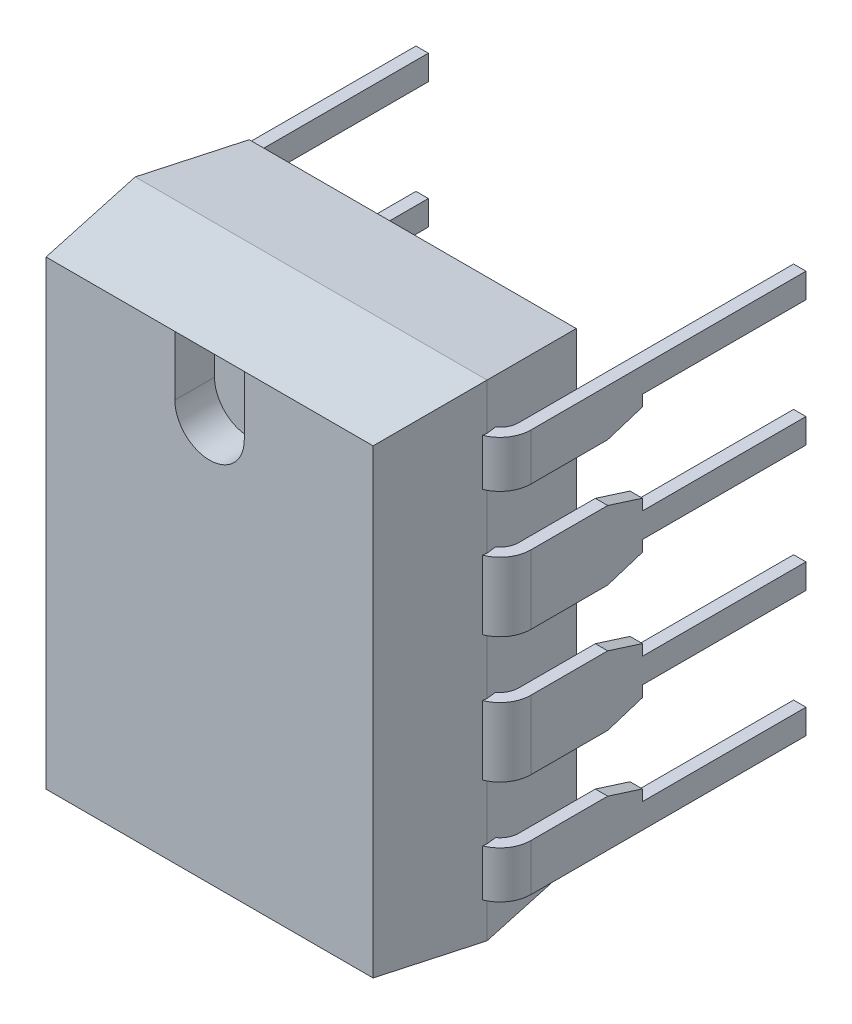
SolidWorks part; units mm, degrees
ref_plane "Front Plane" through (0, 0, 0) normal (0, 0, 1) x (1, 0, 0)
ref_plane "Top Plane" through (0, 0, 0) normal (0, 1, 0) x (1, 0, 0)
ref_plane "Right Plane" through (0, 0, 0) normal (1, 0, 0) x (0, 0, -1)
sketch "Sketch1" plane through (0, 0, 0) normal (0, 1, 0) x (1, 0, 0)
  line L0 (-3.3, -0.7) -> (-3.55, -2.75)
  line L1 (-3.55, -2.75) -> (3.55, -2.75) construction
  line L2 (3.55, -2.75) -> (3.3, -0.7)
  line L3 (3.3, -0.7) -> (-3.3, -0.7)
  line L4 (-3.55, -2.75) -> (-3.3, -4.8)
  line L5 (-3.3, -4.8) -> (3.3, -4.8)
  line L6 (3.3, -4.8) -> (3.55, -2.75)
  line L7 (0, 0) -> (3.3, 0) construction
  line L8 (0, -4.8) -> (0, -0.7) construction
  point P11 (0, -2.75)
  point P12 (0, -0.7)
  point P13 (0, -4.8)
  dimension "D1" = 0.7
  dimension "F" = 7.1
  dimension "D2" = 4.8
  dimension "D4" = 6.6
extrude "Basic Shape" add sketch "Sketch1" along normal mid plane 9.8
sketch "Sketch2" plane through (0, 0, 0) normal (1, 0, 0) x (0, 0, -1)
  line L1 (-4.8, -4.9) -> (-2.75, -4.9) construction
  line L2 (-4.8, 4.9) -> (-4.8, -4.9) construction
  line L3 (-4.8, 4.9) -> (-4.8, 4.65)
  line L4 (-4.8, 4.9) -> (-2.75, 4.9) construction
  line L5 (-4.8, 4.9) -> (-2.75, 4.9)
  line L6 (-2.75, 4.9) -> (-4.8, 4.65)
  line L7 (-4.8, -4.9) -> (-2.75, -4.9)
  line L9 (-2.75, -4.9) -> (-4.8, -4.65)
  line L11 (-4.8, -4.65) -> (-4.8, -4.9)
  dimension "D1" = 0.25
extrude "Side Profile1" cut sketch "Sketch2" against normal through all and the other way through all
sketch "Sketch3" plane through (0, 0, 0) normal (1, 0, 0) x (0, 0, -1)
  line L0 (-2.75, 4.9) -> (-0.7, 4.9) construction
  line L1 (-2.75, 4.9) -> (-0.7, 4.9)
  line L2 (-0.7, 4.9) -> (-0.7, -4.9) construction
  line L3 (-0.7, 4.9) -> (-0.7, 4.65)
  line L4 (-2.75, 4.9) -> (-0.7, 4.65)
  line L5 (-2.75, -4.9) -> (-0.7, -4.9) construction
  line L6 (-2.75, -4.9) -> (-0.7, -4.9)
  line L7 (-2.75, -4.9) -> (-0.7, -4.65)
  line L8 (-0.7, -4.65) -> (-0.7, -4.9)
extrude "Side Profile2" cut sketch "Sketch3" against normal through all and the other way through all
sketch "First Pin Location" plane through (0, 0, 0) normal (1, 0, 0) x (0, 0, -1)
  line L0 (-2.75, 4.9) -> (-2.75, -4.9) construction
  point P0 (-2.75, -4.9)
  point P1 (-2.75, -3.9)
  dimension "Z" = 1
ref_plane "First Pin Plane" through (0, -3.9, 0) normal (0, 1, 0) x (-1, 0, 0)
sketch "Sketch4" plane through (0, 0, 4.8) normal (0, 0, -1) x (-1, 0, 0)
  line L0 (3.3, 4.65) -> (-3.3, 4.65) construction
  line L2 (0.7, 4.65) -> (0.7, 3.45)
  line L3 (-0.7, 3.45) -> (-0.7, 4.65)
  line L5 (0.7, 4.65) -> (-0.7, 4.65)
  arc A0 (0.7, 3.45) -> (-0.7, 3.45) centre (0, 3.45) cw
  dimension "D1" = 1.2
  dimension "D2" = 1.4
extrude "Location Mark" cut sketch "Sketch4" along normal blind 0.8
sketch "Sketch5" plane through (0, -3.9, 0) normal (0, 1, 0) x (1, 0, 0)
  line L0 (-3.55, -2.75) -> (3.55, -2.75) construction
  line L1 (0, -2.75) -> (3.31, -2.75)
  line L2 (3.81, 3.3) -> (3.81, -2.25)
  line L3 (3.81, -2.75) -> (-3.81, -2.75) construction
  arc A0 (3.81, -2.25) -> (3.31, -2.75) centre (3.31, -2.25) cw
  point P0 (-3.81, -2.75)
  point P8 (0, -2.75)
  dimension "D3" = 3.3
  dimension "D2" = 0.5
  dimension "D1" = 7.62
sketch "Sketch6" plane through (0, 0, 0) normal (1, 0, 0) x (0, 0, -1)
  line L0 (-2.875, -3.205) -> (-2.625, -3.205)
  line L1 (-2.875, -3.205) -> (-2.875, -4.595)
  line L2 (-2.625, -4.595) -> (-2.875, -4.595)
  line L3 (-2.625, -4.595) -> (-2.625, -3.205)
  line L4 (-2.625, -3.205) -> (-2.875, -4.595) construction
  point P4 (-2.75, -3.9)
  dimension "D1" = 1.39
  dimension "D2" = 0.25
sweep "First Pin" add profiles "Sketch6" path "Sketch5"
sketch "Sketch7" plane through (3.685, 0, 0) normal (-1, 0, 0) x (0, 0, 1)
  line L0 (-3.3, -4.595) -> (-3.3, -3.205) construction
  line L1 (-3.3, -3.205) -> (-3.3, -4.595) construction
  line L2 (-3.3, -4.15) -> (-3.3, -3.65) construction
  line L3 (-3.3, -4.15) -> (0, -4.15)
  line L5 (-3.3, -3.65) -> (0, -3.65)
  line L6 (0, -3.65) -> (0, -3.4275)
  line L7 (0, -4.15) -> (0, -4.3725)
  line L8 (2.25, -3.205) -> (-3.3, -3.205) construction
  line L9 (0.7, -3.205) -> (-3.3, -3.205)
  line L10 (2.25, -4.595) -> (-3.3, -4.595) construction
  line L11 (0.7, -4.595) -> (-3.3, -4.595)
  line L12 (-3.3, -4.15) -> (-3.3, -4.595)
  line L13 (-3.3, -3.205) -> (-3.3, -3.65)
  line L14 (0, -4.3725) -> (0.7, -4.595)
  line L15 (0.7, 4.65) -> (0.7, -4.65) construction
  line L16 (0, -3.4275) -> (0.7, -3.205)
  point P10 (-3.3, -3.4275)
  dimension "D1" = 0.5
extrude "Pin Relief" cut sketch "Sketch7" against normal through all
mirror "Opp Pin" about plane through (0, 0, 0) normal (1, 0, 0) of "Pin Relief", "First Pin"
pattern_linear "Remaining Pins" count 4 spacing 2.54 along (0, 1, 0) of "First Pin", "Opp Pin", "Pin Relief"
sketch "Sketch9" plane through (0, -4.595, 0) normal (0, -1, 0) x (1, 0, 0)
  line L0 (3.935, 0) -> (3.685, 0) construction
  line L1 (3.935, 0) -> (3.685, 0)
  line L2 (-3.935, 0) -> (-3.685, 0) construction
  line L3 (-3.935, 0) -> (-3.685, 0)
  line L7 (3.685, 2.25) -> (3.685, 0.7)
  line L8 (3.685, 0.7) -> (3.935, 0.7)
  line L9 (3.935, 0.7) -> (3.935, 2.25)
  line L11 (3.5264, 2.5563) -> (3.55, 2.75)
  line L12 (3.55, 2.75) -> (3.5401, 2.8311)
  line L14 (3.685, 2.25) -> (3.685, 0)
  line L16 (3.935, 0) -> (3.935, 2.25)
  line L18 (3.5264, 2.5563) -> (3.55, 2.75)
  line L19 (3.55, 2.75) -> (3.5401, 2.8311)
  line L22 (-3.685, 0.7) -> (-3.685, 2.25)
  line L24 (-3.5401, 2.8311) -> (-3.55, 2.75)
  line L25 (-3.55, 2.75) -> (-3.5264, 2.5563)
  line L27 (-3.935, 2.25) -> (-3.935, 0.7)
  line L28 (-3.935, 0.7) -> (-3.685, 0.7)
  line L29 (-3.685, 0) -> (-3.685, 2.25)
  line L31 (-3.5401, 2.8311) -> (-3.55, 2.75)
  line L32 (-3.55, 2.75) -> (-3.5264, 2.5563)
  line L34 (-3.935, 2.25) -> (-3.935, 0)
  arc A2 (3.935, 2.25) -> (3.5401, 2.8311) centre (3.31, 2.25) ccw
  arc A3 (3.935, 2.25) -> (3.5401, 2.8311) centre (3.31, 2.25) ccw
  arc A4 (3.685, 2.25) -> (3.5264, 2.5563) centre (3.31, 2.25) ccw
  arc A5 (3.685, 2.25) -> (3.5264, 2.5563) centre (3.31, 2.25) ccw
  arc A6 (-3.5264, 2.5563) -> (-3.685, 2.25) centre (-3.31, 2.25) ccw
  arc A7 (-3.5264, 2.5563) -> (-3.685, 2.25) centre (-3.31, 2.25) ccw
  arc A8 (-3.5401, 2.8311) -> (-3.935, 2.25) centre (-3.31, 2.25) ccw
  arc A9 (-3.5401, 2.8311) -> (-3.935, 2.25) centre (-3.31, 2.25) ccw
  dimension "D1" = 0
  dimension "D2" = 0
extrude "Pin Shape1" cut sketch "Sketch9" against normal up to surface (0.445 mm away) up to face at (-3.81, -4.15, -1.65)
sketch "Sketch10" plane through (0, 4.415, 0) normal (0, 1, 0) x (-1, 0, 0)
  line L2 (-3.935, 0) -> (-3.685, 0) construction
  line L3 (-3.935, 0) -> (-3.685, 0)
  line L4 (3.935, 0) -> (3.685, 0) construction
  line L5 (3.935, 0) -> (3.685, 0)
  line L7 (-3.935, 0.7) -> (-3.685, 0.7)
  line L8 (-3.685, 0.7) -> (-3.685, 2.25)
  line L9 (-3.5264, 2.5563) -> (-3.55, 2.75)
  line L10 (-3.55, 2.75) -> (-3.5401, 2.8311)
  line L11 (-3.935, 2.25) -> (-3.935, 0.7)
  line L13 (-3.685, 0) -> (-3.685, 2.25)
  line L14 (-3.5264, 2.5563) -> (-3.55, 2.75)
  line L15 (-3.55, 2.75) -> (-3.5401, 2.8311)
  line L16 (-3.935, 2.25) -> (-3.935, 0)
  line L17 (3.685, 0.7) -> (3.935, 0.7)
  line L18 (3.935, 0.7) -> (3.935, 2.25)
  line L19 (3.5401, 2.8311) -> (3.55, 2.75)
  line L20 (3.55, 2.75) -> (3.5264, 2.5563)
  line L21 (3.685, 2.25) -> (3.685, 0.7)
  line L23 (3.935, 0) -> (3.935, 2.25)
  line L24 (3.5401, 2.8311) -> (3.55, 2.75)
  line L25 (3.55, 2.75) -> (3.5264, 2.5563)
  line L26 (3.685, 2.25) -> (3.685, 0)
  arc A2 (-3.5264, 2.5563) -> (-3.685, 2.25) centre (-3.31, 2.25) ccw
  arc A3 (-3.5401, 2.8311) -> (-3.935, 2.25) centre (-3.31, 2.25) ccw
  arc A4 (-3.5264, 2.5563) -> (-3.685, 2.25) centre (-3.31, 2.25) ccw
  arc A5 (-3.5401, 2.8311) -> (-3.935, 2.25) centre (-3.31, 2.25) ccw
  arc A6 (3.935, 2.25) -> (3.5401, 2.8311) centre (3.31, 2.25) ccw
  arc A7 (3.685, 2.25) -> (3.5264, 2.5563) centre (3.31, 2.25) ccw
  arc A8 (3.935, 2.25) -> (3.5401, 2.8311) centre (3.31, 2.25) ccw
  arc A9 (3.685, 2.25) -> (3.5264, 2.5563) centre (3.31, 2.25) ccw
  dimension "D1" = 0
  dimension "D3" = 0
extrude "Pin Shape2" cut sketch "Sketch10" against normal up to surface (0.445 mm away)
sketch "Component_Outline" plane through (0, 0, 0) normal (0, 0, 1) x (1, 0, 0)
  line L0 (3.55, 4.9) -> (3.55, 3.97)
  line L1 (3.55, 3.97) -> (3.935, 3.97)
  line L2 (3.935, 3.97) -> (3.935, 3.025)
  line L3 (3.935, 3.025) -> (3.55, 3.025)
  line L4 (3.55, 3.025) -> (3.55, 1.875)
  line L5 (3.55, 1.875) -> (3.935, 1.875)
  line L6 (3.935, 1.875) -> (3.935, 0.485)
  line L7 (3.935, 0.485) -> (3.55, 0.485)
  line L8 (3.55, 0.485) -> (3.55, -0.665)
  line L9 (3.55, -0.665) -> (3.935, -0.665)
  line L10 (3.935, -0.665) -> (3.935, -2.055)
  line L11 (3.935, -2.055) -> (3.55, -2.055)
  line L12 (3.5264, -2.055) -> (3.685, -2.055) construction
  line L13 (3.55, -2.055) -> (3.55, -3.205)
  line L14 (3.55, -3.205) -> (3.935, -3.205)
  line L15 (3.935, -3.205) -> (3.935, -4.15)
  line L16 (3.935, -4.15) -> (3.55, -4.15)
  line L17 (3.55, -4.15) -> (3.55, -4.9)
  line L18 (3.55, -4.9) -> (-3.55, -4.9)
  line L19 (-3.55, -4.9) -> (-3.55, -4.15)
  line L20 (-3.55, -4.15) -> (-3.935, -4.15)
  line L21 (-3.935, -4.15) -> (-3.935, -3.205)
  line L22 (-3.935, -3.205) -> (-3.55, -3.205)
  line L23 (-3.55, -3.205) -> (-3.55, -2.055)
  line L24 (-3.55, -2.055) -> (-3.935, -2.055)
  line L25 (-3.935, -2.055) -> (-3.935, -0.665)
  line L26 (-3.935, -0.665) -> (-3.55, -0.665)
  line L27 (-3.55, -0.665) -> (-3.55, 0.485)
  line L28 (-3.55, 0.485) -> (-3.935, 0.485)
  line L29 (-3.935, 0.485) -> (-3.935, 1.875)
  line L30 (-3.935, 1.875) -> (-3.55, 1.875)
  line L31 (-3.55, 1.875) -> (-3.55, 3.025)
  line L32 (-3.55, 3.025) -> (-3.935, 3.025)
  line L33 (-3.935, 3.025) -> (-3.935, 3.97)
  line L34 (-3.935, 3.97) -> (-3.55, 3.97)
  line L35 (-3.55, 3.97) -> (-3.55, 4.9)
  line L36 (-3.55, 4.9) -> (3.55, 4.9)
  line L37 (-3.55, 3.97) -> (-3.935, 3.025) construction
  point P49 (-3.7425, 3.4975)
